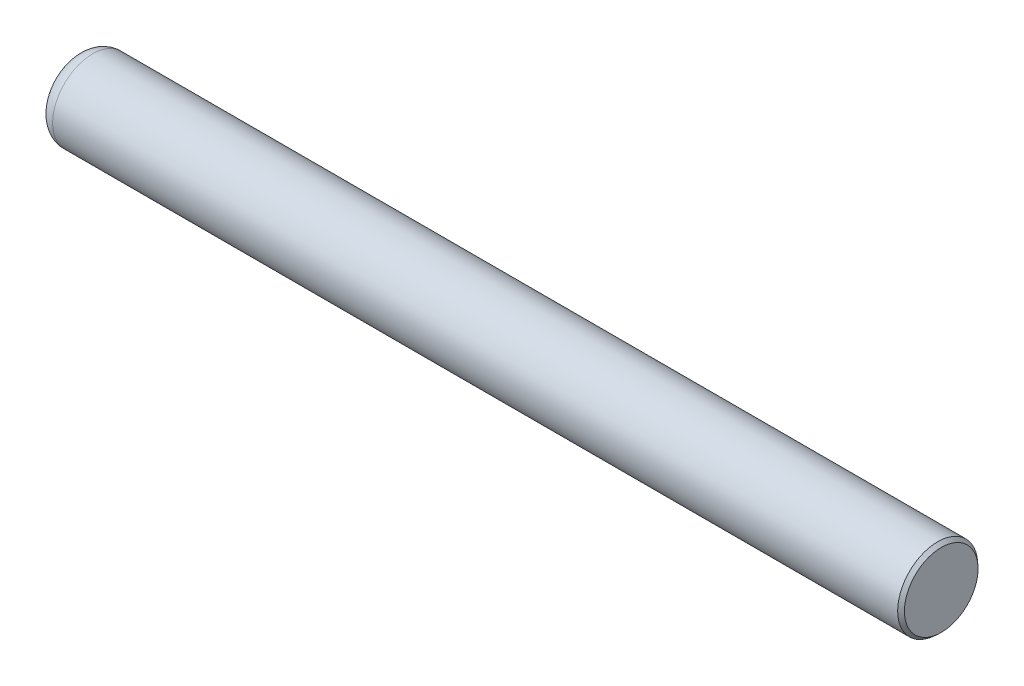
SolidWorks part; units mm, degrees
ref_plane "Ön Düzlem" through (0, 0, 0) normal (0, 0, 1) x (1, 0, 0)
ref_plane "Üst Düzlem" through (0, 0, 0) normal (0, 1, 0) x (1, 0, 0)
ref_plane "Sağ Düzlem" through (0, 0, 0) normal (1, 0, 0) x (0, 0, -1)
sketch "Çizim1" plane through (0, 0, 0) normal (0, 0, 1) x (1, 0, 0)
  line L0 (0, 25) -> (540, 25)
  line L2 (0, 25) -> (0, 50)
  line L3 (0, 50) -> (540, 50)
  line L4 (540, 25) -> (540, 50)
  dimension "D1" = 540
  dimension "D2" = 25
revolve "Döndür1" add sketch "Çizim1" angle 360 about L0
chamfer "Pah1" distance 2 angle 48 1 edges at (540, 25, 25)
fillet "Radyus1" radius 10 1 edges at (0, 25, 25)
